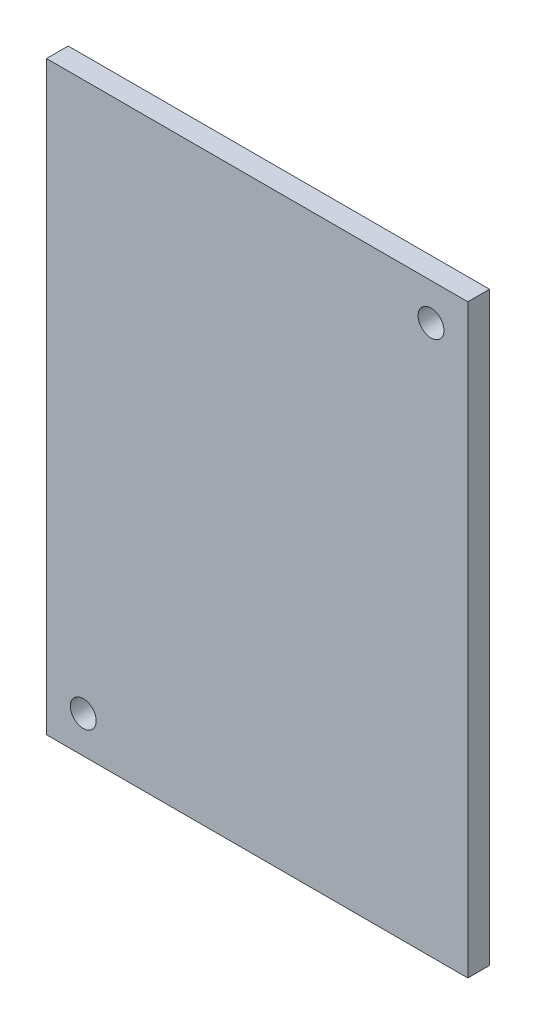
SolidWorks part; units mm, degrees
ref_plane "Front Plane" through (0, 0, 0) normal (1, 0, 0) x (0, 1, 0)
ref_plane "Top Plane" through (0, 0, 0) normal (0, 0, 1) x (0, 1, 0)
ref_plane "Right Plane" through (0, 0, 0) normal (0, 1, 0) x (-1, 0, 0)
sketch "Sketch2" plane through (0, 0, 0) normal (0, 0, 1) x (0, 1, 0)
  line L1 (-40.43, -29.085) -> (40.43, -29.085)
  line L2 (-40.43, -29.085) -> (-40.43, 29.085)
  line L3 (-40.43, 29.085) -> (40.43, 29.085)
  line L4 (40.43, -29.085) -> (40.43, 29.085)
  line L5 (-40.43, -29.085) -> (40.43, 29.085) construction
  line L6 (-40.43, 29.085) -> (40.43, -29.085) construction
  point P0 (0, 0)
  dimension "D1" = 58.17
  dimension "D2" = 80.86
extrude "Boss-Extrude1" add sketch "Sketch2" along normal blind 2.9972
sketch "Sketch3" plane through (0, 0, 2.9972) normal (0, 0, 1) x (1, 0, 0)
  line L0 (29.085, 40.43) -> (-29.085, 40.43) construction
  line L1 (29.085, -40.43) -> (29.085, 40.43) construction
  line L2 (-29.085, -40.43) -> (29.085, -40.43) construction
  line L3 (-29.085, 40.43) -> (-29.085, -40.43) construction
  point P0 (24.005, 35.35)
  point P1 (-24.005, -35.35)
  dimension "D1" = 5.08
  dimension "D2" = 5.08
  dimension "D3" = 5.08
  dimension "D4" = 5.08
hole_wizard "9/64 (0.14063) Diameter Hole1" positions "Sketch4" profile "Sketch5" hole size "9/64" standard "ANSI Inch" end condition through all
sketch "Sketch4" plane through (0, 0, 2.9972) normal (0, 0, 1) x (1, 0, 0)
  point P0 (24.005, 35.35)
  point P3 (-24.005, -35.35)
sketch "Sketch5" plane through (24.005, 35.35, 2.9972) normal (1, 0, 0) x (0, -1, 0)
  line L0 (0, 0) -> (0, 2.9972)
  line L1 (0, 2.9972) -> (1.786, 2.9972)
  line L2 (1.786, 2.9972) -> (1.786, 0)
  line L5 (1.786, 0) -> (0, 0)
  line L11 (0, -6.35) -> (0, 107.95) construction
  dimension "Thru Hole Dia." = 3.572
  dimension "Thru Hole Depth" = 2.9972
